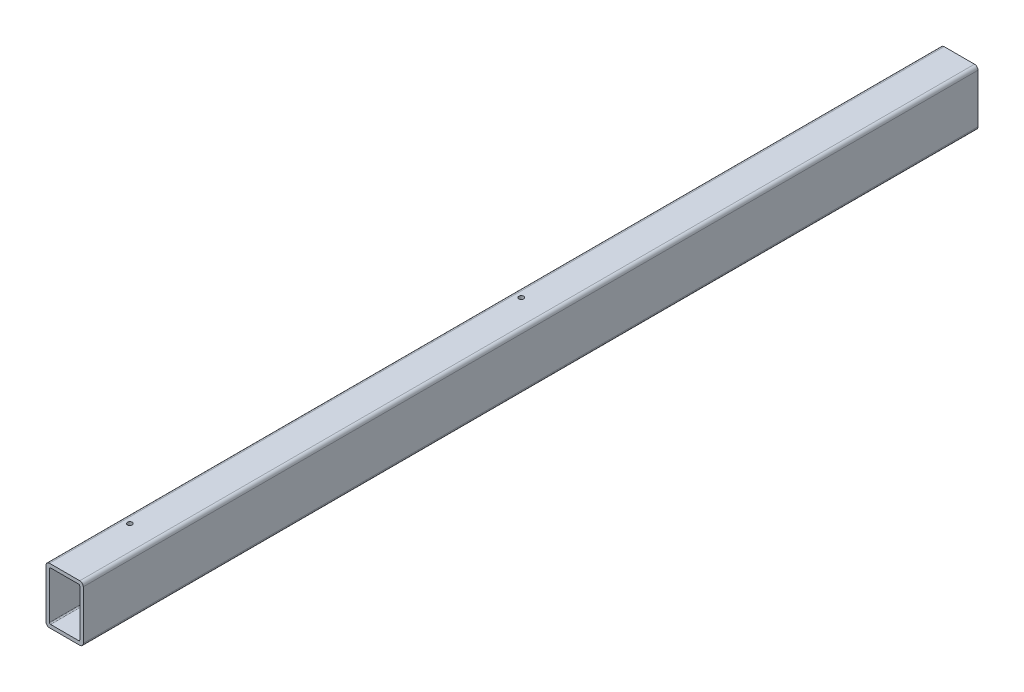
SolidWorks part; units mm, degrees
ref_plane "Front Plane" through (0, 0, 0) normal (0, 0, 1) x (1, 0, 0)
ref_plane "Top Plane" through (0, 0, 0) normal (0, 1, 0) x (1, 0, 0)
ref_plane "Right Plane" through (0, 0, 0) normal (1, 0, 0) x (0, 0, -1)
sketch "Sketch1" plane through (0, 0, 0) normal (0, 0, 1) x (1, 0, 0)
  line L1 (-20.6375, 38.1) -> (20.6375, 38.1)
  line L2 (-25.4, 33.3375) -> (-25.4, -33.3375)
  line L3 (-20.6375, -38.1) -> (20.6375, -38.1)
  line L4 (25.4, 33.3375) -> (25.4, -33.3375)
  line L5 (-25.4, 38.1) -> (25.4, -38.1) construction
  line L6 (-25.4, -38.1) -> (25.4, 38.1) construction
  line L7 (-19.05, 33.3375) -> (19.05, 33.3375)
  line L8 (-20.6375, 31.75) -> (-20.6375, -31.75)
  line L9 (-19.05, -33.3375) -> (19.05, -33.3375)
  line L10 (20.6375, 31.75) -> (20.6375, -31.75)
  line L11 (-20.6375, 33.3375) -> (20.6375, -33.3375) construction
  line L12 (-20.6375, -33.3375) -> (20.6375, 33.3375) construction
  arc A0 (-25.4, -33.3375) -> (-20.6375, -38.1) centre (-20.6375, -33.3375) ccw
  arc A1 (20.6375, -38.1) -> (25.4, -33.3375) centre (20.6375, -33.3375) ccw
  arc A2 (25.4, 33.3375) -> (20.6375, 38.1) centre (20.6375, 33.3375) ccw
  arc A3 (-20.6375, 38.1) -> (-25.4, 33.3375) centre (-20.6375, 33.3375) ccw
  arc A4 (-20.6375, -31.75) -> (-19.05, -33.3375) centre (-19.05, -31.75) ccw
  arc A5 (19.05, -33.3375) -> (20.6375, -31.75) centre (19.05, -31.75) ccw
  arc A6 (20.6375, 31.75) -> (19.05, 33.3375) centre (19.05, 31.75) ccw
  arc A7 (-19.05, 33.3375) -> (-20.6375, 31.75) centre (-19.05, 31.75) ccw
  point P0 (0, 0)
  point P6 (0, 0)
  dimension "D4" = 4.7625
  dimension "D5" = 1.5875
  dimension "D1" = 76.2
  dimension "D2" = 50.8
  dimension "D3" = 4.7625
  dimension "D6" = 4.7625
extrude "Boss-Extrude1" add sketch "Sketch1" along normal mid plane 1219.2
sketch "Sketch2" plane through (0, -38.1, 0) normal (0, -1, 0) x (1, 0, 0)
  line L0 (0, 609.6) -> (0, -609.6) construction
  line L1 (-20.6375, 609.6) -> (20.6375, 609.6) construction
  line L2 (-20.6375, -609.6) -> (20.6375, -609.6) construction
  line L3 (-25.4, -584.2) -> (25.4, -584.2) construction
  line L4 (-25.4, 609.6) -> (-25.4, -609.6) construction
  line L5 (25.4, 609.6) -> (25.4, -609.6) construction
  line L6 (-25.4, 50.8) -> (25.4, 50.8) construction
  line L7 (-25.4, 527.05) -> (25.4, 527.05) construction
  dimension "D1" = 25.4
  dimension "D2" = 635
  dimension "D3" = 82.55
sketch "Sketch3" plane through (-25.4, 0, 0) normal (-1, 0, 0) x (0, 0, 1)
  line L0 (-609.6, 0) -> (609.6, 0) construction
  line L1 (-609.6, 33.3375) -> (-609.6, -33.3375) construction
  line L2 (609.6, 33.3375) -> (609.6, -33.3375) construction
  line L3 (-584.2, 38.1) -> (-584.2, -38.1) construction
  line L4 (609.6, 38.1) -> (-609.6, 38.1) construction
  line L5 (609.6, -38.1) -> (-609.6, -38.1) construction
  line L6 (-355.6, 38.1) -> (-355.6, -38.1) construction
  line L7 (-177.8, 38.1) -> (-177.8, -38.1) construction
  line L8 (584.2, 38.1) -> (584.2, -38.1) construction
  dimension "D1" = 25.4
  dimension "D2" = 25.4
  dimension "D3" = 228.6
  dimension "D4" = 177.8
sketch "Sketch4" plane through (0, 0, 609.6) normal (0, 0, 1) x (1, 0, 0)
  line L0 (25.4, 0) -> (-25.4, 0) construction
  line L1 (25.4, -33.3375) -> (25.4, 33.3375) construction
  line L2 (-25.4, 33.3375) -> (-25.4, -33.3375) construction
hole_wizard "5/16-18 Tapped Hole1" positions "Sketch7" profile "Sketch6" tap size "5/16-18" standard "ANSI Inch" end condition up to next
sketch "Sketch7" plane through (0, 38.1, 0) normal (0, 1, 0) x (1, 0, 0)
  line L0 (-12.7, 25.4) -> (-12.7, -508) construction
  line L1 (20.6375, -609.6) -> (-20.6375, -609.6) construction
  line L2 (-25.4, -609.6) -> (-25.4, 609.6) construction
  point P0 (-12.7, -508)
  point P2 (-12.7, 25.4)
  dimension "D1" = 101.6
  dimension "D2" = 12.7
  dimension "D3" = 533.4
sketch "Sketch6" plane through (-12.7, 38.1, 508) normal (1, 0, 0) x (0, 0, 1)
  line L0 (0, 0) -> (0, 4.7625)
  line L1 (0, 4.7625) -> (3.2639, 4.7625)
  line L2 (3.2639, 4.7625) -> (3.2639, 0)
  line L5 (3.2639, 0) -> (0, 0)
  line L11 (0, -6.35) -> (0, 107.95) construction
  dimension "Thread Major Dia." = 6.5278
  dimension "Thru Tap Drill Depth" = 4.7625
ref_plane "Plane1" through (228.6, 0, 0) normal (1, 0, 0) x (0, 0, -1)
